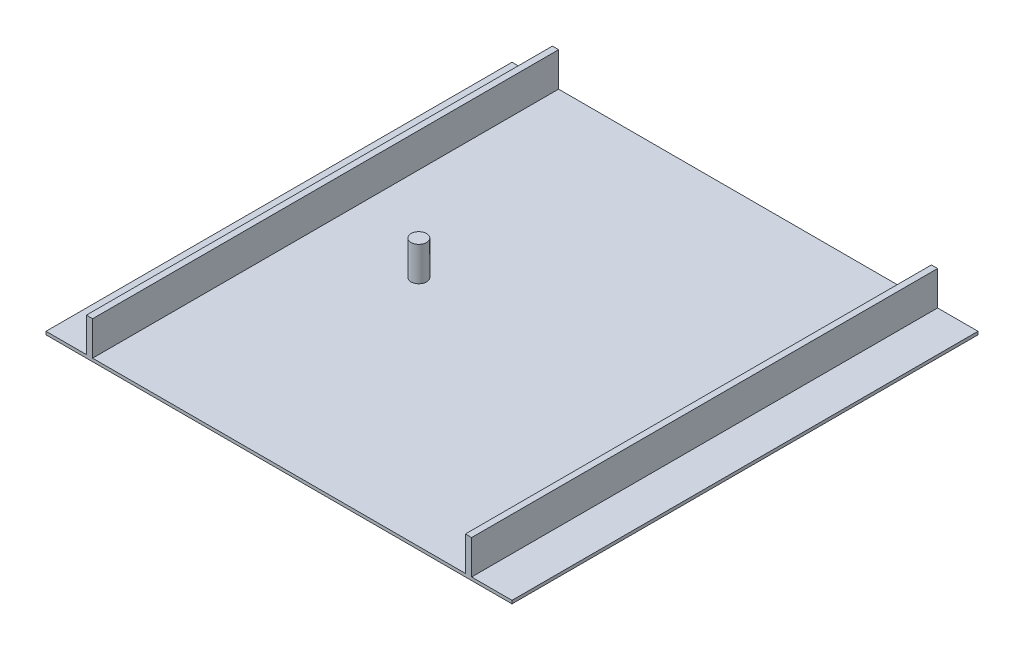
SolidWorks part; units mm, degrees
ref_plane "Front Plane" through (0, 0, 0) normal (0, 0, 1) x (1, 0, 0)
ref_plane "Top Plane" through (0, 0, 0) normal (0, 1, 0) x (1, 0, 0)
ref_plane "Right Plane" through (0, 0, 0) normal (1, 0, 0) x (0, 0, -1)
sketch "Sketch2" plane through (0, 0, 0) normal (0, 1, 0) x (1, 0, 0)
  line L1 (-750, 750) -> (750, 750)
  line L2 (-750, 750) -> (-750, -750)
  line L3 (-750, -750) -> (750, -750)
  line L4 (750, 750) -> (750, -750)
  line L5 (-750, 750) -> (750, -750) construction
  line L6 (-750, -750) -> (750, 750) construction
  point P0 (0, 0)
  dimension "D1" = 1500
  dimension "D2" = 1500
extrude "Boss-Extrude1" add sketch "Sketch2" along normal blind 10
sketch "Sketch3" plane through (0, 10, 0) normal (0, 1, 0) x (1, 0, 0)
  line L0 (620, 750) -> (620, -750) construction
  line L1 (750, 750) -> (-750, 750) construction
  line L2 (-750, -750) -> (750, -750) construction
  line L3 (600, 750) -> (600, -750) construction
  line L4 (750, -750) -> (750, 750) construction
  line L5 (-750, -600) -> (750, -600) construction
  line L6 (-750, 750) -> (-750, -750) construction
  line L7 (-750, -620) -> (750, -620) construction
  line L8 (-750, 0) -> (750, 0) construction
  line L9 (0, 750) -> (0, -750) construction
  line L10 (-750, 620) -> (750, 620) construction
  line L11 (-750, 600) -> (750, 600) construction
  line L12 (-620, 750) -> (-620, -750) construction
  line L13 (-600, 750) -> (-600, -750) construction
  line L15 (-620, 750) -> (-600, 750)
  line L16 (-620, 750) -> (-620, -750)
  line L17 (-620, -750) -> (-600, -750)
  line L18 (-600, 750) -> (-600, -750)
  line L19 (600, 750) -> (620, 750)
  line L20 (600, 750) -> (600, -750)
  line L21 (600, -750) -> (620, -750)
  line L22 (620, 750) -> (620, -750)
  dimension "D6" = 150
  dimension "D5" = 20
  dimension "D7" = 20
  dimension "D8" = 150
extrude "Boss-Extrude2" add sketch "Sketch3" along normal blind 110
sketch "Sketch4" plane through (0, 10, 0) normal (0, 1, 0) x (1, 0, 0)
  line L0 (-600, 0) -> (0, 0) construction
  line L1 (-600, -750) -> (-600, 750) construction
  circle A0 centre (-300, 0) radius 25
  dimension "D1" = 50
extrude "Boss-Extrude3" add sketch "Sketch4" along normal up to surface (110 mm away) up to face at (-610, 120, 0)
equation "\"CellSize\"=1500"
equation "\"D1@Sketch2\"=\"CellSize\""
equation "\"D2@Sketch2\"=\"CellSize\""
equation "\"TrackWidth\"= 1200"
equation "\"C\"=342.079"
equation "\"WallWidth\"=20"
equation "\"D6@Sketch3\"=\"EdgeWidth\""
equation "\"D5@Sketch3\"=\"WallWidth\""
equation "\"D7@Sketch3\"=\"WallWidth\""
equation "\"EdgeWidth\"= ( \"CellSize\" - \"TrackWidth\" ) / 2"
equation "\"D8@Sketch3\"=\"EdgeWidth\""
